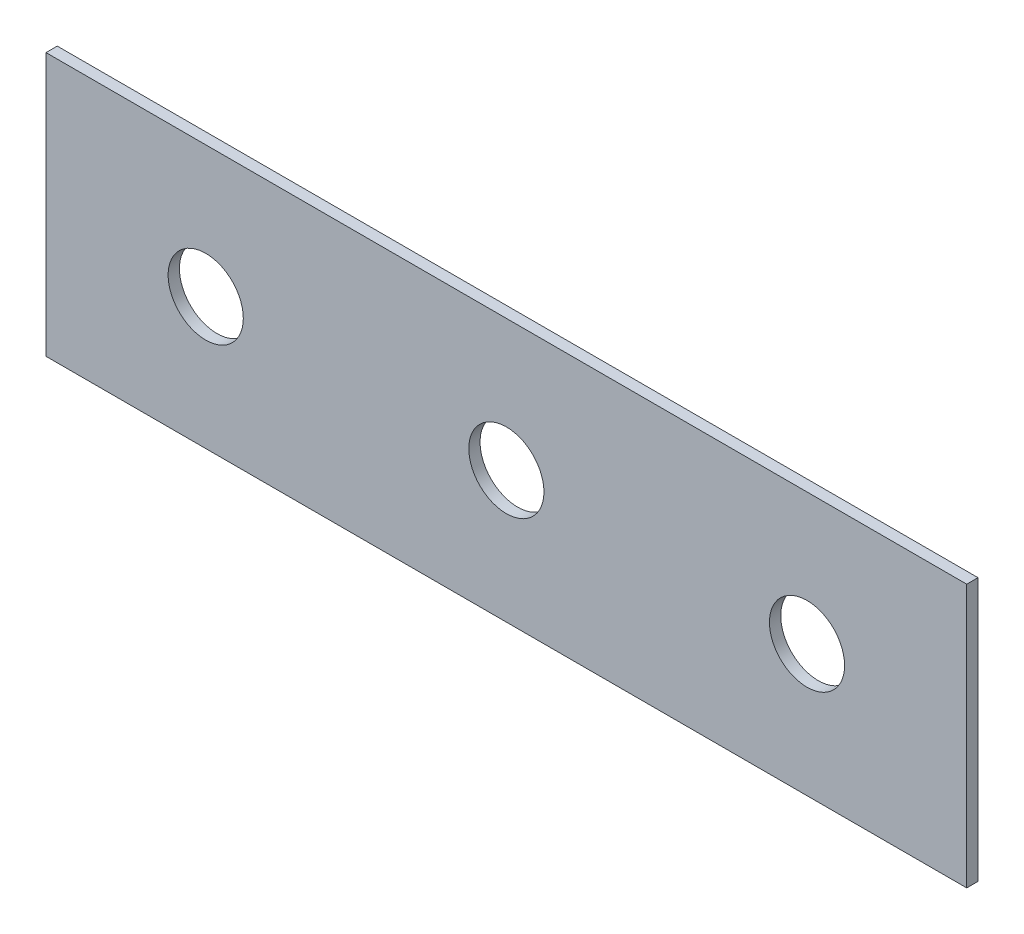
SolidWorks part; units mm, degrees
ref_plane "Front Plane" through (0, 0, 0) normal (0, 0, 1) x (1, 0, 0)
ref_plane "Top Plane" through (0, 0, 0) normal (0, 1, 0) x (1, 0, 0)
ref_plane "Right Plane" through (0, 0, 0) normal (1, 0, 0) x (0, 0, -1)
sketch "Sketch1" plane through (0, 0, 0) normal (0, 0, 1) x (1, 0, 0)
  line L1 (-122.5, 35) -> (122.5, 35)
  line L2 (-122.5, 35) -> (-122.5, -35)
  line L3 (-122.5, -35) -> (122.5, -35)
  line L4 (122.5, 35) -> (122.5, -35)
  line L5 (-122.5, 35) -> (122.5, -35) construction
  line L6 (-122.5, -35) -> (122.5, 35) construction
  point P0 (0, 0)
  dimension "D1" = 245
  dimension "D2" = 70
extrude "Boss-Extrude1" add sketch "Sketch1" along normal blind 3
sketch "Sketch2" plane through (0, 0, 3) normal (0, 0, 1) x (1, 0, 0)
  circle A0 centre (-80, 0) radius 10
  circle A1 centre (0, 0) radius 10
  circle A2 centre (80, 0) radius 10
  dimension "D3" = 20
  dimension "D4" = 20
  dimension "D5" = 20
  dimension "D1" = 80
  dimension "D2" = 80
extrude "Cut-Extrude1" cut sketch "Sketch2" against normal blind 3
